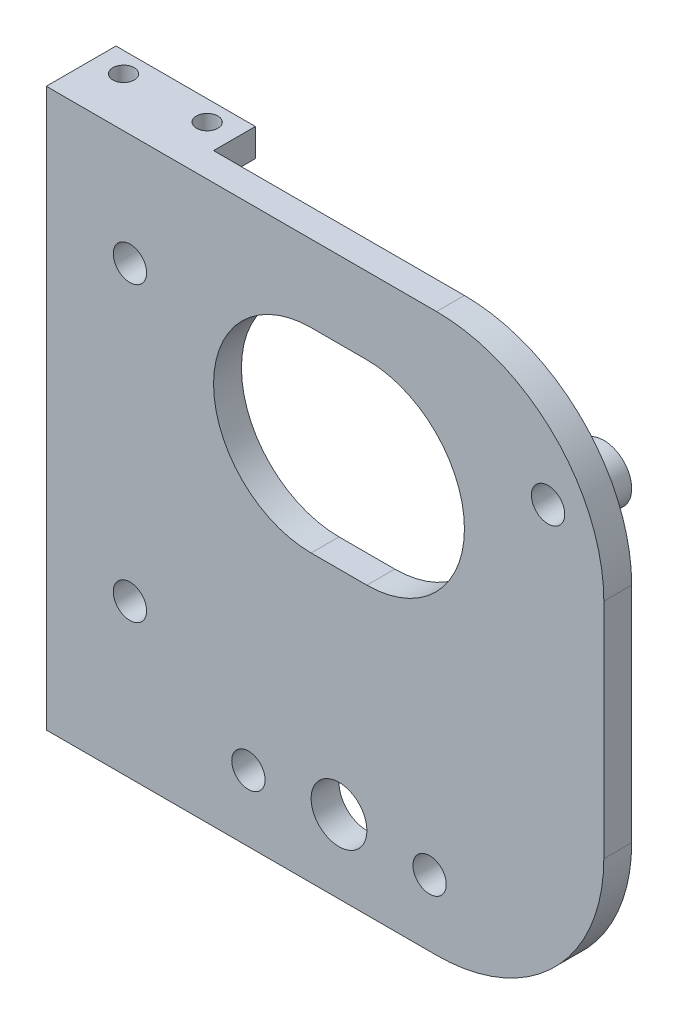
SolidWorks part; units mm, degrees
material "Polycarbonate"
ref_plane "Front Plane" through (0, 0, 0) normal (0, 0, 1) x (1, 0, 0)
ref_plane "Top Plane" through (0, 0, 0) normal (0, 1, 0) x (1, 0, 0)
ref_plane "Right Plane" through (0, 0, 0) normal (1, 0, 0) x (0, 0, -1)
sketch "Sketch1" plane through (0, 0, 0) normal (0, 0, 1) x (1, 0, 0)
  line L1 (-31.75, 31.75) -> (31.75, 31.75)
  line L2 (-31.75, 31.75) -> (-31.75, -31.75)
  line L3 (-31.75, -31.75) -> (31.75, -31.75)
  line L4 (31.75, 31.75) -> (31.75, -31.75)
  line L5 (-31.75, 31.75) -> (31.75, -31.75) construction
  line L6 (-31.75, -31.75) -> (31.75, 31.75) construction
  point P0 (0, 0)
  dimension "D1" = 63.5
  dimension "D2" = 63.5
extrude "Boss-Extrude1" add sketch "Sketch1" along normal blind 3.175
sketch "Sketch2" plane through (0, 0, 0) normal (0, 0, -1) x (-1, 0, 0)
  line L0 (31.75, -31.75) -> (-31.75, -31.75) construction
  line L1 (15.875, -31.75) -> (25.4, -31.75)
  line L2 (15.875, -31.75) -> (15.875, -28.595)
  line L3 (15.875, -28.595) -> (25.7558, -28.595)
  line L8 (31.75, -31.75) -> (25.4, -31.75)
  line L9 (31.75, -31.75) -> (31.75, -28.595)
  line L10 (31.75, -28.595) -> (25.7558, -28.595)
  dimension "D1" = 3.175
  dimension "D2" = 15.875
extrude "Boss-Extrude2" add sketch "Sketch2" along normal blind 4.7625
hole_wizard "#2 Clearance Hole2" positions "Sketch5" profile "Sketch6" hole size "#2" standard "ANSI Inch" end condition up to next
sketch "Sketch5" plane through (0, -28.595, 0) normal (0, 1, 0) x (1, 0, 0)
  line L0 (-31.75, 4.7625) -> (-31.75, 0) construction
  line L1 (-15.875, 4.7625) -> (-15.875, 0) construction
  point P0 (-28.575, 2.4476)
  point P2 (-19.05, 2.4476)
  dimension "D1" = 3.175
  dimension "D2" = 3.175
sketch "Sketch6" plane through (-28.575, -28.595, -2.4476) normal (1, 0, 0) x (0, 0, 1)
  line L0 (0, 0) -> (0, 3.155)
  line L1 (0, 3.155) -> (1.2192, 3.155)
  line L2 (1.2192, 3.155) -> (1.2192, 0)
  line L5 (1.2192, 0) -> (0, 0)
  line L11 (0, -6.35) -> (0, 107.95) construction
  dimension "Thru Hole Dia." = 2.4384
  dimension "Thru Hole Depth" = 3.155
fillet "Fillet1" radius 19.05 2 edges at (31.75, 31.75, 1.5875) (31.75, -31.75, 1.5875)
sketch "Sketch7" plane through (0, 0, 0) normal (0, 0, -1) x (-1, 0, 0)
  line L0 (15.875, -28.595) -> (15.875, -31.75) construction
  line L1 (31.75, 31.75) -> (15.875, 31.75)
  line L2 (31.75, 31.75) -> (31.75, 28.575)
  line L3 (31.75, 28.575) -> (15.875, 28.575)
  line L4 (15.875, 31.75) -> (15.875, 28.575)
  dimension "D1" = 3.175
extrude "Boss-Extrude3" add sketch "Sketch7" along normal blind 4.7625
hole_wizard "#2 Clearance Hole3" positions "Sketch8" profile "Sketch9" hole size "#2" standard "ANSI Inch" end condition up to next
sketch "Sketch8" plane through (0, 31.75, 0) normal (0, 1, 0) x (1, 0, 0)
  line L0 (12.7, -3.175) -> (-31.75, -3.175) construction
  line L1 (-31.75, -3.175) -> (-31.75, 4.7625) construction
  line L2 (-15.875, 4.7625) -> (-15.875, 0) construction
  point P0 (-28.575, 2.4476)
  point P3 (-19.05, 2.4476)
  dimension "D1" = 5.6226
  dimension "D2" = 3.175
  dimension "D3" = 5.6226
  dimension "D4" = 3.175
sketch "Sketch9" plane through (-28.575, 31.75, -2.4476) normal (1, 0, 0) x (0, 0, 1)
  line L0 (0, 0) -> (0, 3.175)
  line L1 (0, 3.175) -> (1.2192, 3.175)
  line L2 (1.2192, 3.175) -> (1.2192, 0)
  line L5 (1.2192, 0) -> (0, 0)
  line L11 (0, -6.35) -> (0, 107.95) construction
  dimension "Thru Hole Dia." = 2.4384
  dimension "Thru Hole Depth" = 3.175
sketch "Sketch10" plane through (0, 0, 3.175) normal (0, 0, 1) x (1, 0, 0)
  line L0 (-22.225, 19.05) -> (-22.225, -14.2875) construction
  line L1 (-22.225, -14.2875) -> (-8.7313, -24.2094) construction
  line L2 (-8.7313, -24.2094) -> (11.9062, -24.2094) construction
  line L3 (11.9062, -24.2094) -> (25.4, -24.2094) construction
  line L4 (25.4, -24.2094) -> (25.4, 19.05) construction
  line L5 (25.4, 19.05) -> (-22.225, 19.05) construction
  line L6 (-31.75, 31.75) -> (-31.75, -31.75) construction
  line L7 (12.7, 31.75) -> (-31.75, 31.75) construction
  circle A0 centre (25.4, 19.05) radius 3.175
  circle A1 centre (-22.225, 19.05) radius 3.175
  circle A2 centre (-22.225, -14.2875) radius 3.175
  circle A3 centre (-8.7313, -24.2094) radius 3.175
  circle A4 centre (11.9062, -24.2094) radius 3.175
  dimension "D1" = 6.35
  dimension "D2" = 9.525
  dimension "D3" = 47.625
  dimension "D4" = 43.2594
  dimension "D5" = 13.4938
  dimension "D6" = 20.6375
  dimension "D7" = 33.3375
  dimension "D8" = 12.7
extrude "Boss-Extrude4" add sketch "Sketch10" against normal blind 3.175 from surface at -3.175 starting at face at (-3.0209, -0.004, 0)
hole_wizard "#6 Clearance Hole1" positions "Sketch11" profile "Sketch12" hole size "#6" standard "ANSI Inch" end condition through all
sketch "Sketch11" plane through (0, 0, -3.175) normal (0, 0, -1) x (-1, 0, 0)
  point P0 (-25.4, 19.05)
  point P3 (22.225, 19.05)
  point P6 (22.225, -14.2875)
  point P9 (8.7313, -24.2094)
  point P12 (-11.9062, -24.2094)
sketch "Sketch12" plane through (25.4, 19.05, -3.175) normal (1, 0, 0) x (0, 1, 0)
  line L0 (0, 0) -> (0, 6.35)
  line L1 (0, 6.35) -> (1.8986, 6.35)
  line L2 (1.8986, 6.35) -> (1.8986, 0)
  line L5 (1.8986, 0) -> (0, 0)
  line L11 (0, -6.35) -> (0, 107.95) construction
  dimension "Thru Hole Dia." = 3.7973
  dimension "Thru Hole Depth" = 6.35
sketch "Sketch13" plane through (0, 0, 3.175) normal (0, 0, 1) x (1, 0, 0)
  line L0 (-22.225, 19.05) -> (25.4, 19.05) construction
  line L1 (12.7, 31.75) -> (-31.75, 31.75) construction
  line L2 (-12.7, 0.7938) -> (15.875, 0.7938) construction
  line L3 (-12.7, 0.7938) -> (-12.7, 23.0188) construction
  line L4 (-12.7, 23.0188) -> (15.875, 23.0188) construction
  line L5 (15.875, 0.7938) -> (15.875, 23.0188) construction
  line L6 (-1.5875, 11.9063) -> (4.7625, 11.9063) construction
  line L7 (-1.5875, 23.0188) -> (4.7625, 23.0188)
  line L8 (-1.5875, 0.7938) -> (4.7625, 0.7938)
  arc A0 (-1.5875, 23.0188) -> (-1.5875, 0.7938) centre (-1.5875, 11.9063) ccw
  arc A1 (4.7625, 0.7938) -> (4.7625, 23.0188) centre (4.7625, 11.9063) ccw
  circle A2 centre (1.5875, -23.4156) radius 3.175
  circle A4 centre (-8.7313, -24.2094) radius 1.8986 construction
  point P8 (1.5875, 23.0188)
  point P9 (1.5875, 19.05)
  point P14 (1.5875, 11.9063)
  dimension "D4" = 6.35
  dimension "D1" = 8.7312
  dimension "D2" = 28.575
  dimension "D3" = 22.225
  dimension "D5" = 0.7937
extrude "Cut-Extrude1" cut sketch "Sketch13" against normal blind 3.175
